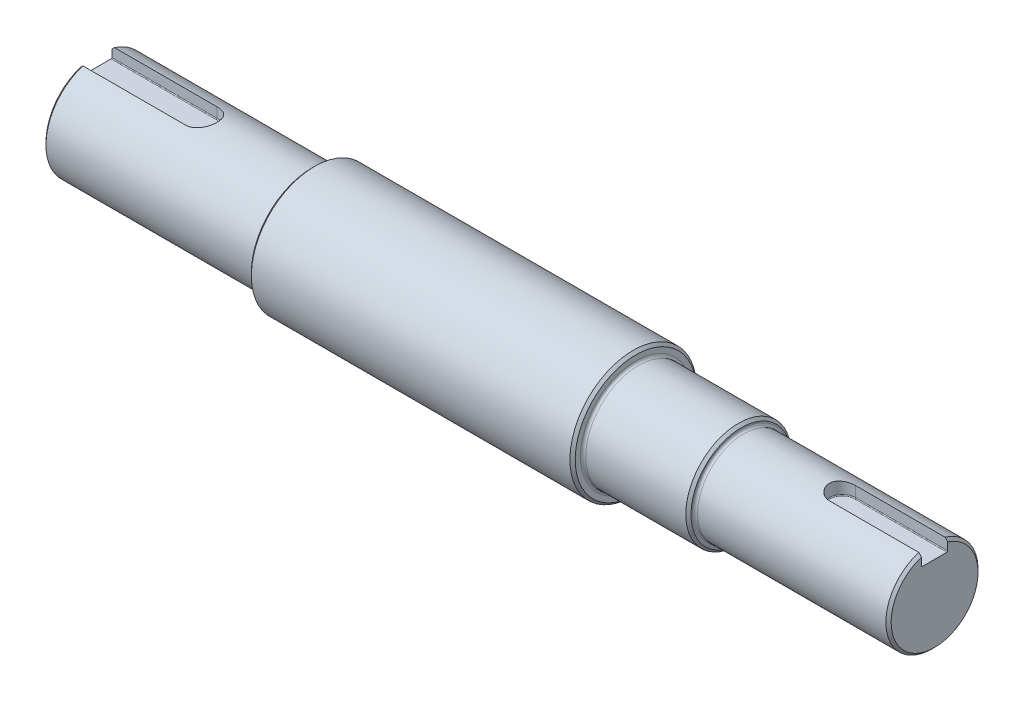
SolidWorks part; units mm, degrees
material "AISI 1045 Steel, cold drawn"
ref_plane "Front Plane" through (0, 0, 0) normal (0, 0, 1) x (1, 0, 0)
ref_plane "Top Plane" through (0, 0, 0) normal (0, 1, 0) x (1, 0, 0)
ref_plane "Right Plane" through (0, 0, 0) normal (1, 0, 0) x (0, 0, -1)
sketch "Sketch1" plane through (0, 0, 0) normal (0, 0, 1) x (1, 0, 0)
  line L0 (-150, 0) -> (-150, 20)
  line L1 (-150, 20) -> (-68, 20)
  line L2 (-68, 20) -> (-68, 24)
  line L3 (-68, 24) -> (55, 24)
  line L4 (55, 24) -> (55, 20)
  line L5 (55, 20) -> (95, 20)
  line L6 (95, 20) -> (95, 17.5)
  line L7 (-150, 0) -> (34, 0)
  line L8 (95, 17.5) -> (168.5, 17.5)
  line L9 (168.5, 17.5) -> (168.5, 0)
  line L10 (168.5, 0) -> (34, 0)
  dimension "D1" = 20
  dimension "D2" = 82
  dimension "D3" = 123
  dimension "D4" = 20
  dimension "D5" = 17.5
  dimension "D6" = 40
  dimension "D7" = 73.5
  dimension "D8" = 24
revolve "Revolve1" add sketch "Sketch1" angle 360 about L7
ref_plane "Plane1" through (0, 20, 0) normal (0, 1, 0) x (1, 0, 0)
sketch "Sketch2" plane through (0, 20, 0) normal (0, 1, 0) x (1, 0, 0)
  line L0 (-150, 20) -> (-150, -20) construction
  line L1 (-150, 0) -> (-110, 0)
  line L2 (-150, 6) -> (-150, -6)
  line L3 (-150, -6) -> (-110, -6)
  line L5 (-150, 6) -> (-110, 6)
  arc A0 (-110, -6) -> (-110, 6) centre (-110, 0) ccw
  dimension "D1" = 6
  dimension "D2" = 40
extrude "Cut-Extrude1" cut sketch "Sketch2" against normal blind 5
fillet "Fillet1" radius 0.3 3 edges at (-130, 15, 6) (-104, 15, 0) (-130, 15, -6)
ref_plane "Plane2" through (0, 17.5, 0) normal (0, 1, 0) x (1, 0, 0)
sketch "Sketch3" plane through (0, 17.5, 0) normal (0, 1, 0) x (1, 0, 0)
  line L0 (168.5, -17.5) -> (168.5, 17.5) construction
  line L1 (168.5, 0) -> (133.5, 0)
  line L2 (168.5, -5) -> (168.5, 5)
  line L3 (168.5, 5) -> (133.5, 5)
  line L5 (168.5, -5) -> (133.5, -5)
  arc A0 (133.5, 5) -> (133.5, -5) centre (133.5, 0) ccw
  dimension "D3" = 5
  dimension "D1" = 35
  dimension "D2" = 10
extrude "Cut-Extrude2" cut sketch "Sketch3" against normal blind 5
fillet "Fillet2" radius 0.3 3 edges at (151, 12.5, 5) (128.5, 12.5, 0) (151, 12.5, -5)
chamfer "Chamfer1" distance 1 angle 45 5 edges at (168.5, -17.5, 0) (95, -20, 0) (55, -24, 0) (-68, -24, 0) (-150, -20, 0)
fillet "Fillet3" radius 1 3 edges at (95, -17.5, 0) (55, -20, 0) (-68, -20, 0)
